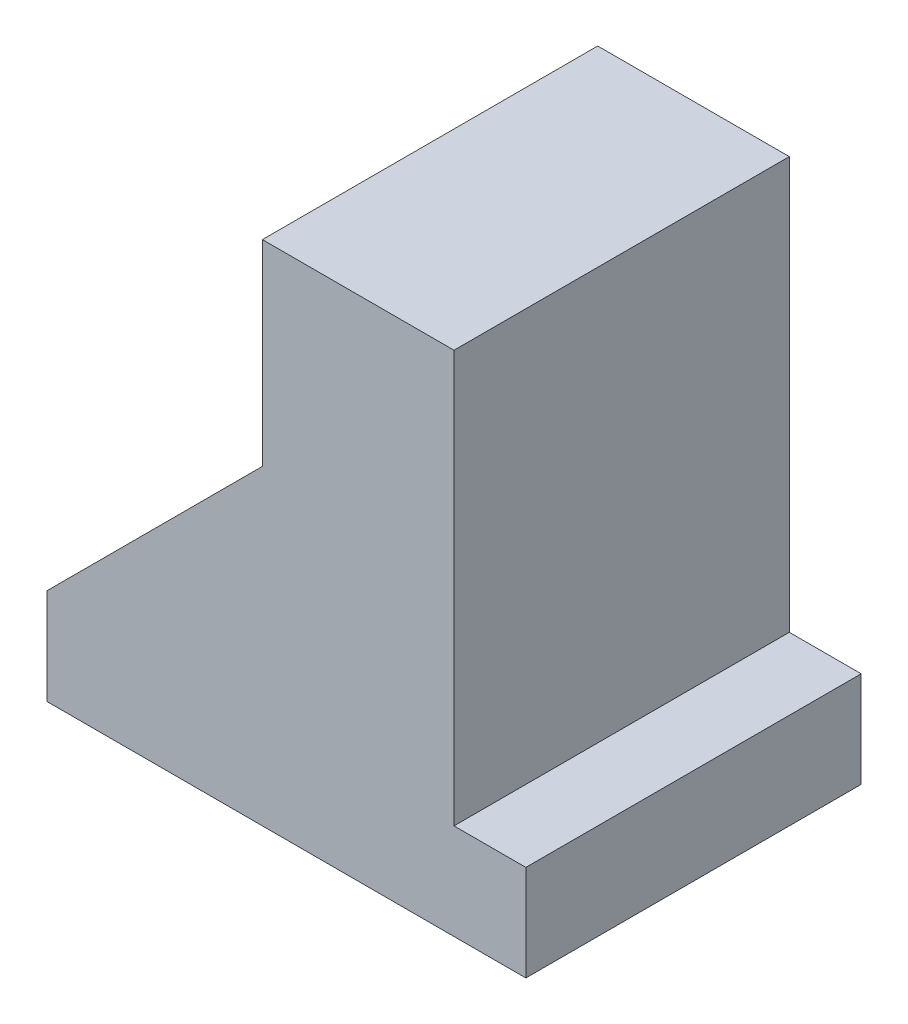
SolidWorks part; units mm, degrees
ref_plane "Front Plane" through (0, 0, 0) normal (0, 0, 1) x (1, 0, 0)
ref_plane "Top Plane" through (0, 0, 0) normal (0, 1, 0) x (1, 0, 0)
ref_plane "Right Plane" through (0, 0, 0) normal (1, 0, 0) x (0, 0, -1)
sketch "Sketch1" plane through (0, 0, 0) normal (0, 0, 1) x (1, 0, 0)
  line L0 (0, 0) -> (12.7, 0)
  line L1 (12.7, 0) -> (12.7, 2.54)
  line L2 (12.7, 2.54) -> (10.795, 2.54)
  line L3 (10.795, 2.54) -> (10.795, 13.462)
  line L4 (10.795, 13.462) -> (5.715, 13.462)
  line L5 (5.715, 13.462) -> (5.715, 8.255)
  line L6 (5.715, 8.255) -> (0, 2.54)
  line L8 (0, 2.54) -> (0, 0)
  dimension "D1" = 1.905
  dimension "D2" = 2.54
  dimension "D3" = 10.922
  dimension "D4" = 12.7
  dimension "D5" = 5.08
  dimension "D6" = 45
  dimension "D7" = 2.54
extrude "Boss-Extrude1" add sketch "Sketch1" along normal blind 8.89
